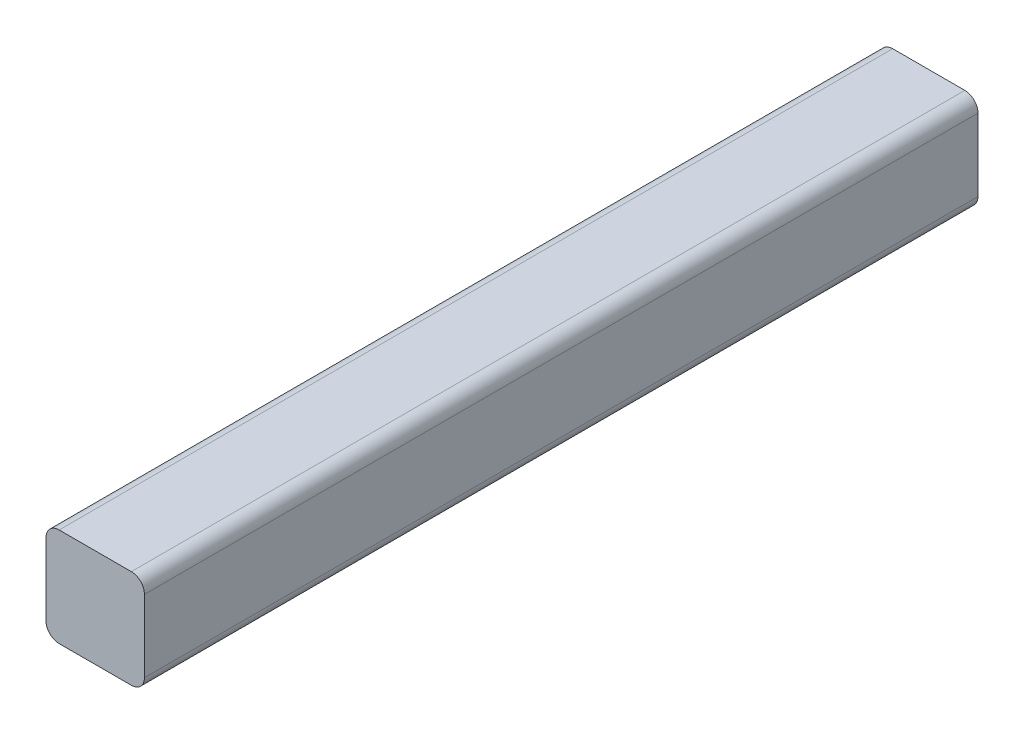
SolidWorks part; units mm, degrees
ref_plane "Front Plane" through (0, 0, 0) normal (0, 0, 1) x (1, 0, 0)
ref_plane "Top Plane" through (0, 0, 0) normal (0, 1, 0) x (1, 0, 0)
ref_plane "Right Plane" through (0, 0, 0) normal (1, 0, 0) x (0, 0, -1)
sketch "Sketch1" plane through (0, 0, 0) normal (0, 0, 1) x (1, 0, 0)
  line L1 (7.5, -7.5) -> (-7.5, -7.5)
  line L2 (7.5, -7.5) -> (7.5, 7.5)
  line L3 (7.5, 7.5) -> (-7.5, 7.5)
  line L4 (-7.5, -7.5) -> (-7.5, 7.5)
  line L5 (7.5, -7.5) -> (-7.5, 7.5) construction
  line L6 (7.5, 7.5) -> (-7.5, -7.5) construction
  point P0 (0, 0)
  dimension "D1" = 15
  dimension "D2" = 15
extrude "Boss-Extrude1" add sketch "Sketch1" along normal blind 127
fillet "Fillet1" radius 2 4 edges at (-7.5, -7.5, 63.5) (7.5, -7.5, 63.5) (-7.5, 7.5, 63.5) (7.5, 7.5, 63.5)
